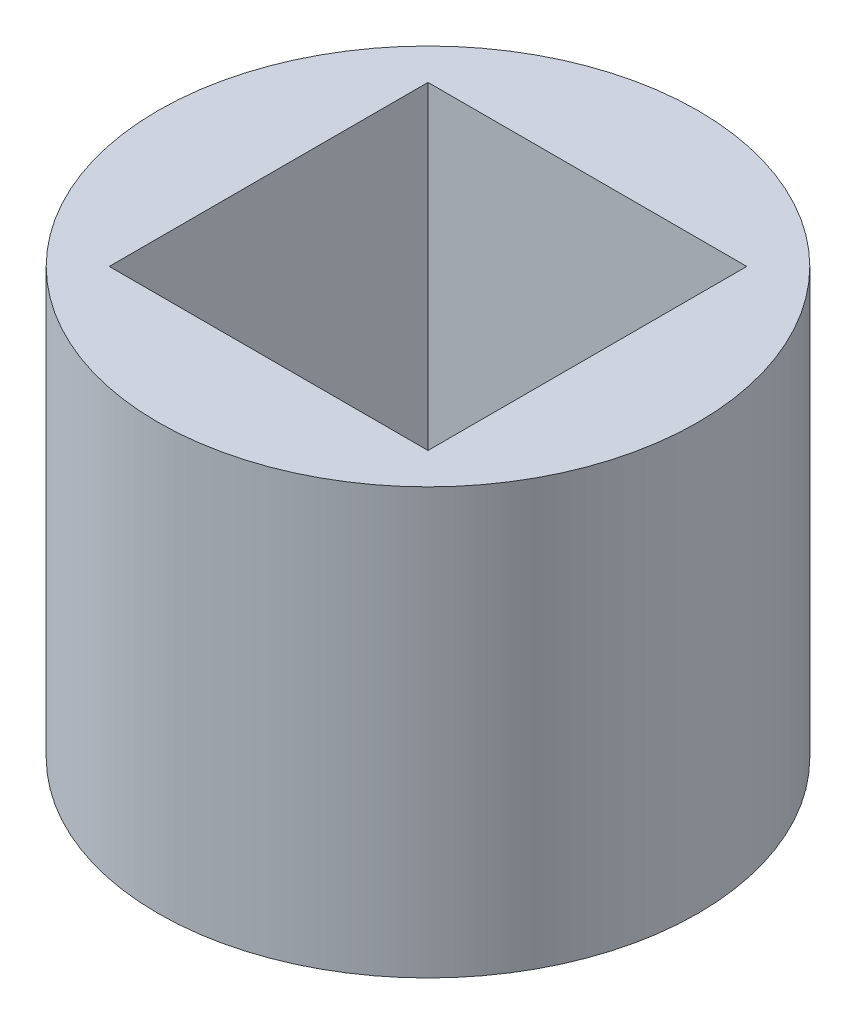
SolidWorks part; units mm, degrees
ref_plane "Front Plane" through (0, 0, 0) normal (0, 0, 1) x (1, 0, 0)
ref_plane "Top Plane" through (0, 0, 0) normal (0, 1, 0) x (1, 0, 0)
ref_plane "Right Plane" through (0, 0, 0) normal (1, 0, 0) x (0, 0, -1)
sketch "Sketch1" plane through (0, 0, 0) normal (0, 1, 0) x (1, 0, 0)
  line L1 (-7.495, 7.495) -> (7.495, 7.495)
  line L2 (-7.495, 7.495) -> (-7.495, -7.495)
  line L3 (-7.495, -7.495) -> (7.495, -7.495)
  line L4 (7.495, 7.495) -> (7.495, -7.495)
  line L5 (-7.495, 7.495) -> (7.495, -7.495) construction
  line L6 (-7.495, -7.495) -> (7.495, 7.495) construction
  circle A0 centre (0, 0) radius 12.695
  dimension "D1" = 25.39
  dimension "D2" = 14.99
  dimension "D3" = 14.99
extrude "Boss-Extrude2" add sketch "Sketch1" along normal blind 20
